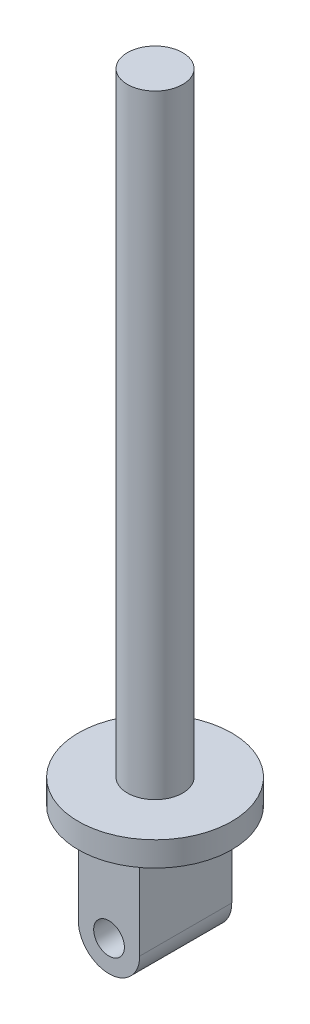
SolidWorks part; units mm, degrees
ref_plane "Plano frontal" through (0, 0, 0) normal (0, 0, 1) x (1, 0, 0)
ref_plane "Plano superior" through (0, 0, 0) normal (0, 1, 0) x (1, 0, 0)
ref_plane "Plano direito" through (0, 0, 0) normal (1, 0, 0) x (0, 0, -1)
sketch "Esboço1" plane through (0, 0, 0) normal (0, 0, 1) x (1, 0, 0)
  line L0 (0, 0) -> (0, 285.6589) construction
  line L1 (0, 0) -> (379.0859, 0) construction
  line L2 (0, 200) -> (9, 200)
  line L3 (9, 200) -> (9, 0)
  line L5 (0, 0) -> (0, 200)
  line L6 (9, 0) -> (25, 0)
  line L7 (25, 0) -> (25, -8)
  line L8 (25, -8) -> (0, -8)
  line L9 (0, -8) -> (0, 0)
  dimension "D1" = 200
  dimension "D2" = 18
  dimension "D3" = 8
  dimension "D4" = 50
revolve "Revolução1" add sketch "Esboço1" angle 360 about L0
sketch "Esboço3" plane through (0, 0, 0) normal (0, 0, 1) x (1, 0, 0)
  line L0 (-10, -8) -> (10, -8)
  line L1 (-25, -8) -> (25, -8) construction
  line L2 (10, -8) -> (10, -38)
  line L3 (0, -8) -> (0, -51) construction
  line L4 (-10, -8) -> (-10, -38)
  arc A0 (-10, -38) -> (10, -38) centre (0, -38) ccw
  circle A1 centre (0, -38) radius 5
  dimension "D1" = 20
  dimension "D3" = 10
  dimension "D2" = 30
extrude "Ressalto-extrusão1" add sketch "Esboço3" along normal mid plane 30
